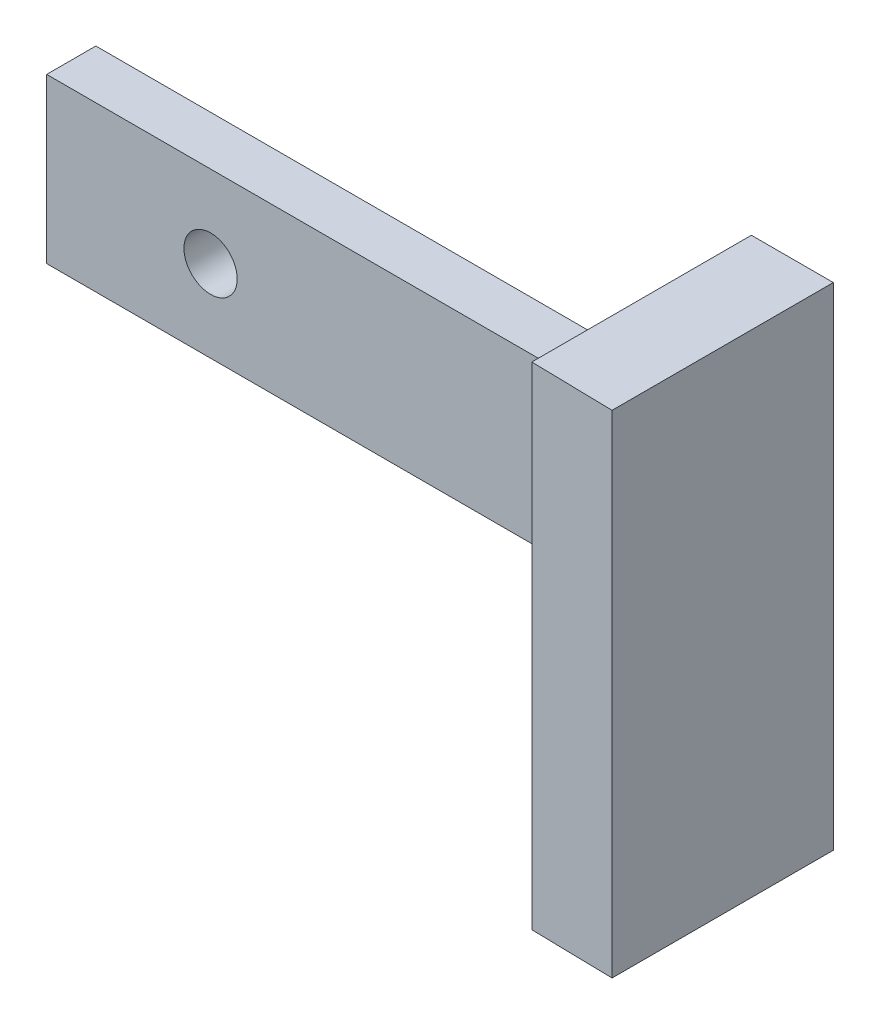
SolidWorks part; units mm, degrees
ref_plane "Plan de face" through (0, 0, 0) normal (0, 0, 1) x (1, 0, 0)
ref_plane "Plan de dessus" through (0, 0, 0) normal (0, 1, 0) x (1, 0, 0)
ref_plane "Plan de droite" through (0, 0, 0) normal (1, 0, 0) x (0, 0, -1)
sketch "Esquisse1" plane through (0, 0, 0) normal (0, 0, 1) x (1, 0, 0)
  line L1 (-5, 0) -> (40, 0)
  line L2 (-5, 0) -> (-5, -10)
  line L3 (-5, -10) -> (40, -10)
  line L4 (40, 0) -> (40, -10)
  dimension "D1" = 45
  dimension "D2" = 10
extrude "Boss.-Extru.1" add sketch "Esquisse1" along normal blind 3
sketch "Esquisse2" plane through (0, 0, 3) normal (0, 0, 1) x (1, 0, 0)
  line L0 (-5, 0) -> (-5, -10) construction
  circle A0 centre (30, -5) radius 1.625
  circle A1 centre (5, -5) radius 1.625
  point P4 (0, 0)
  point P7 (-5, -5)
  dimension "D2" = 3.25
  dimension "D3" = 3.25
  dimension "D1" = 25
  dimension "D4" = 10
extrude "Enlèv. mat.-Extru.1" cut sketch "Esquisse2" against normal through all
sketch "Esquisse3" plane through (0, -10, 0) normal (0, -1, 0) x (1, 0, 0)
  line L0 (-5, 0) -> (40, 0) construction
  line L1 (40, 3) -> (35, 3)
  line L2 (40, 3) -> (40, 0)
  line L3 (40, 0) -> (35, 0)
  line L4 (35, 3) -> (35, 0)
  dimension "D1" = 5
extrude "Boss.-Extru.2" add sketch "Esquisse3" along normal blind 10 and the other way blind 20
sketch "Esquisse4" plane through (0, 0, 3) normal (0, 0, 1) x (1, 0, 0)
  line L1 (40, 10) -> (35, 10)
  line L2 (40, 10) -> (40, -20)
  line L3 (40, -20) -> (35, -20)
  line L4 (35, 10) -> (35, -20)
extrude "Boss.-Extru.3" add sketch "Esquisse4" along normal blind 10.5
sketch "Esquisse5" plane through (0, -20, 0) normal (0, -1, 0) x (1, 0, 0)
  line L0 (35, 13.5) -> (40, 13.5)
  line L1 (40, 13.5) -> (35, 13.4)
  line L2 (35, 13.5) -> (35, 0) construction
  line L3 (35, 13.4) -> (35, 13.5)
  dimension "D1" = 0.1
extrude "Enlèv. mat.-Extru.2" cut sketch "Esquisse5" against normal through all
